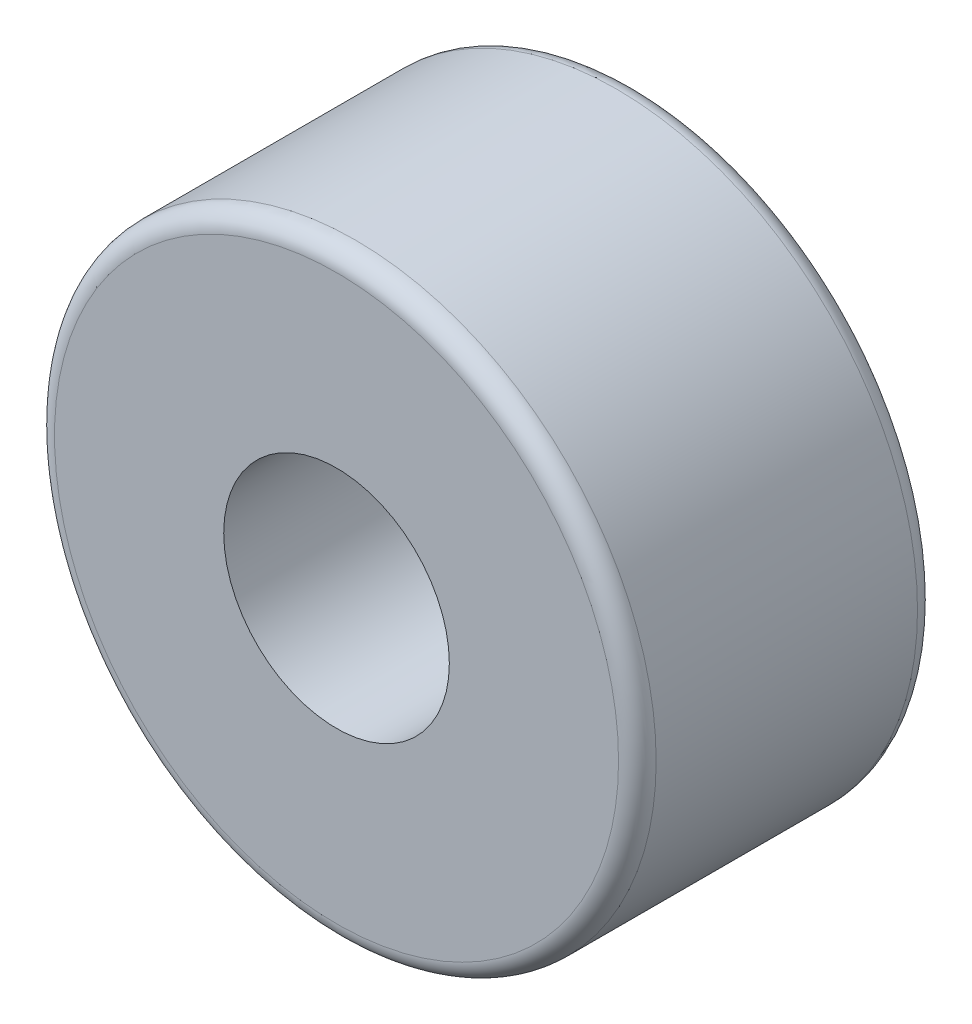
SolidWorks part; units mm, degrees
material "AISI 4340 Steel, annealed"
ref_plane "Front Plane" through (0, 0, 0) normal (0, 0, 1) x (1, 0, 0)
ref_plane "Top Plane" through (0, 0, 0) normal (0, 1, 0) x (1, 0, 0)
ref_plane "Right Plane" through (0, 0, 0) normal (1, 0, 0) x (0, 0, -1)
sketch "Sketch1" plane through (0, 0, 0) normal (0, 0, 1) x (1, 0, 0)
  circle A0 centre (0, 0) radius 6
  circle A1 centre (0, 0) radius 16
  dimension "D1" = 12
  dimension "D2" = 32
extrude "Boss-Extrude1" add sketch "Sketch1" along normal blind 15.9
fillet "Fillet1" radius 1 2 edges at (16, 0, 0) (16, 0, 15.9)
